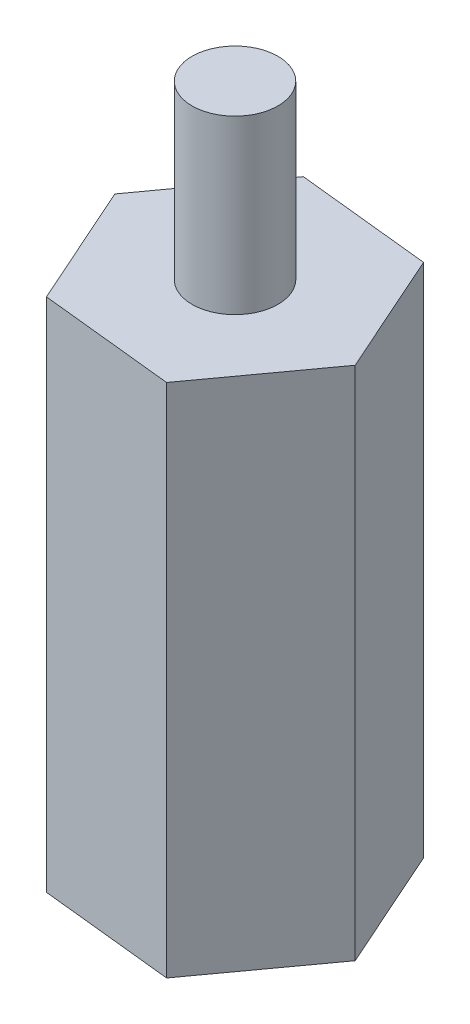
SolidWorks part; units mm, degrees
ref_plane "Front Plane" through (0, 0, 0) normal (0, 0, 1) x (1, 0, 0)
ref_plane "Top Plane" through (0, 0, 0) normal (0, 1, 0) x (1, 0, 0)
ref_plane "Right Plane" through (0, 0, 0) normal (1, 0, 0) x (0, 0, -1)
sketch "Sketch1" plane through (0, 0, 0) normal (0, 1, 0) x (1, 0, 0)
  line L1 (2.3073, 3.1766) -> (-1.5974, 3.5865)
  line L2 (-1.5974, 3.5865) -> (-3.9047, 0.4099)
  line L3 (-3.9047, 0.4099) -> (-2.3073, -3.1766)
  line L4 (-2.3073, -3.1766) -> (1.5974, -3.5865)
  line L5 (1.5974, -3.5865) -> (3.9047, -0.4099)
  line L6 (3.9047, -0.4099) -> (2.3073, 3.1766)
  circle A0 centre (0, 0) radius 1.25
  circle A1 centre (0, 0) radius 3.4001 construction
extrude "Boss-Extrude1" add sketch "Sketch1" along normal blind 15
sketch "Sketch2" plane through (0, 15, 0) normal (0, 1, 0) x (1, 0, 0)
  circle A0 centre (0, 0) radius 1.25
extrude "Boss-Extrude2" add sketch "Sketch2" along normal blind 5 separate body
